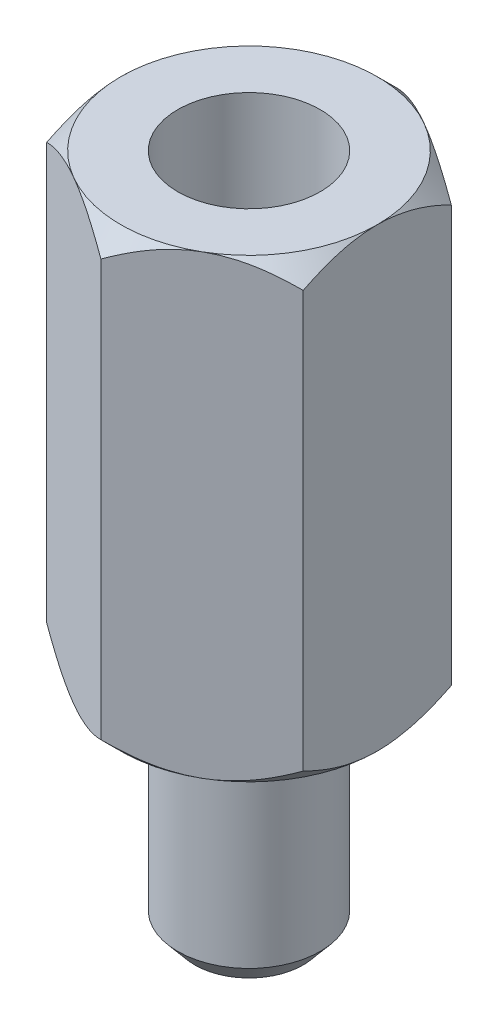
SolidWorks part; units mm, degrees
ref_plane "Front Plane" through (0, 0, 0) normal (0, 0, 1) x (1, 0, 0)
ref_plane "Top Plane" through (0, 0, 0) normal (0, 1, 0) x (1, 0, 0)
ref_plane "Right Plane" through (0, 0, 0) normal (1, 0, 0) x (0, 0, -1)
sketch "Sketch1" plane through (0, 0, 0) normal (0, 1, 0) x (1, 0, 0)
  circle A0 centre (0, 0) radius 1.25
  dimension "D1" = 2.5
extrude "Boss-Extrude1" add sketch "Sketch1" along normal blind 3.9
sketch "Sketch2" plane through (0, 3.9, 0) normal (0, 1, 0) x (1, 0, 0)
  line L1 (0, 2.5981) -> (-2.25, 1.299)
  line L2 (-2.25, 1.299) -> (-2.25, -1.299)
  line L3 (-2.25, -1.299) -> (0, -2.5981)
  line L4 (0, -2.5981) -> (2.25, -1.299)
  line L5 (2.25, -1.299) -> (2.25, 1.299)
  line L6 (2.25, 1.299) -> (0, 2.5981)
  circle A0 centre (0, 0) radius 2.25 construction
  dimension "D1" = 4.5
extrude "Boss-Extrude2" add sketch "Sketch2" along normal blind 8
sketch "Sketch3" plane through (0, 11.9, 0) normal (0, 1, 0) x (1, 0, 0)
  circle A0 centre (0, 0) radius 1.25
  dimension "D1" = 2.5
extrude "Cut-Extrude1" cut sketch "Sketch3" against normal blind 4.8
sketch "Sketch4" plane through (0, 11.9, 0) normal (0, 1, 0) x (1, 0, 0)
  circle A0 centre (0, 0) radius 2.25
extrude "Cut-Extrude2" cut sketch "Sketch4" against normal blind 4.8 draft 45 flip side to cut
sketch "Sketch5" plane through (0, 3.9, 0) normal (0, -1, 0) x (1, 0, 0)
  circle A0 centre (0, 0) radius 2.25
extrude "Cut-Extrude3" cut sketch "Sketch5" against normal through all draft 45 flip side to cut
chamfer "Chamfer1" distance 0.3 angle 50 1 edges at (0, 0, 1.25)
